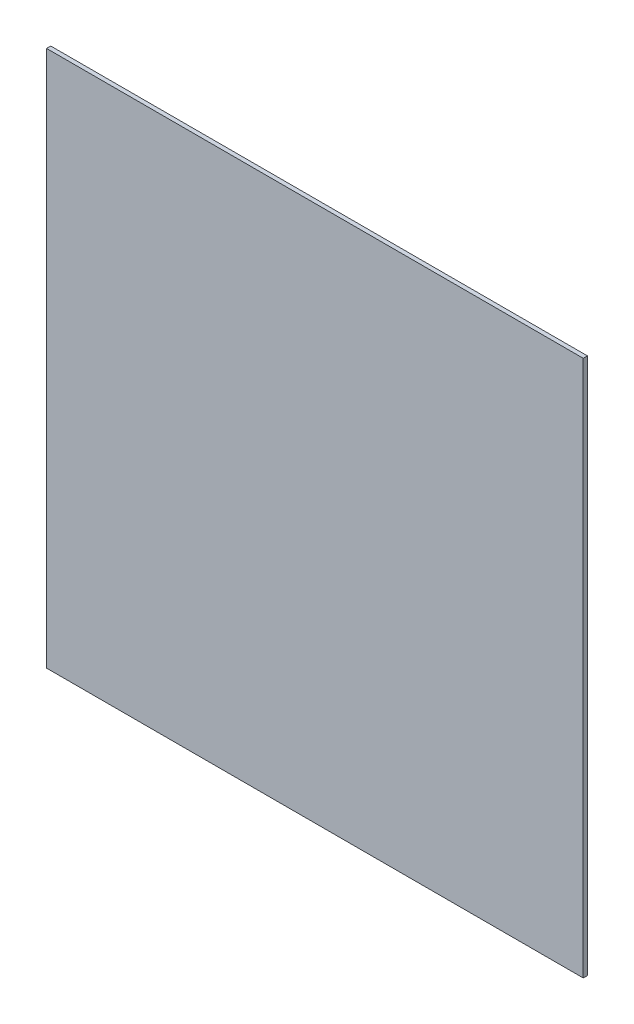
SolidWorks part; units mm, degrees
ref_plane "Front Plane" through (0, 0, 0) normal (0, 0, 1) x (1, 0, 0)
ref_plane "Top Plane" through (0, 0, 0) normal (0, 1, 0) x (1, 0, 0)
ref_plane "Right Plane" through (0, 0, 0) normal (1, 0, 0) x (0, 0, -1)
sketch "Sketch1" plane through (0, 0, 0) normal (0, 0, 1) x (1, 0, 0)
  line L0 (0, 0) -> (0, 1219.2)
  line L1 (0, 0) -> (1219.2, 0)
  line L2 (1219.2, 0) -> (1219.2, 1219.2)
  line L3 (1219.2, 1219.2) -> (0, 1219.2)
extrude "Boss-Extrude1" add sketch "Sketch1" along normal blind 9.525
